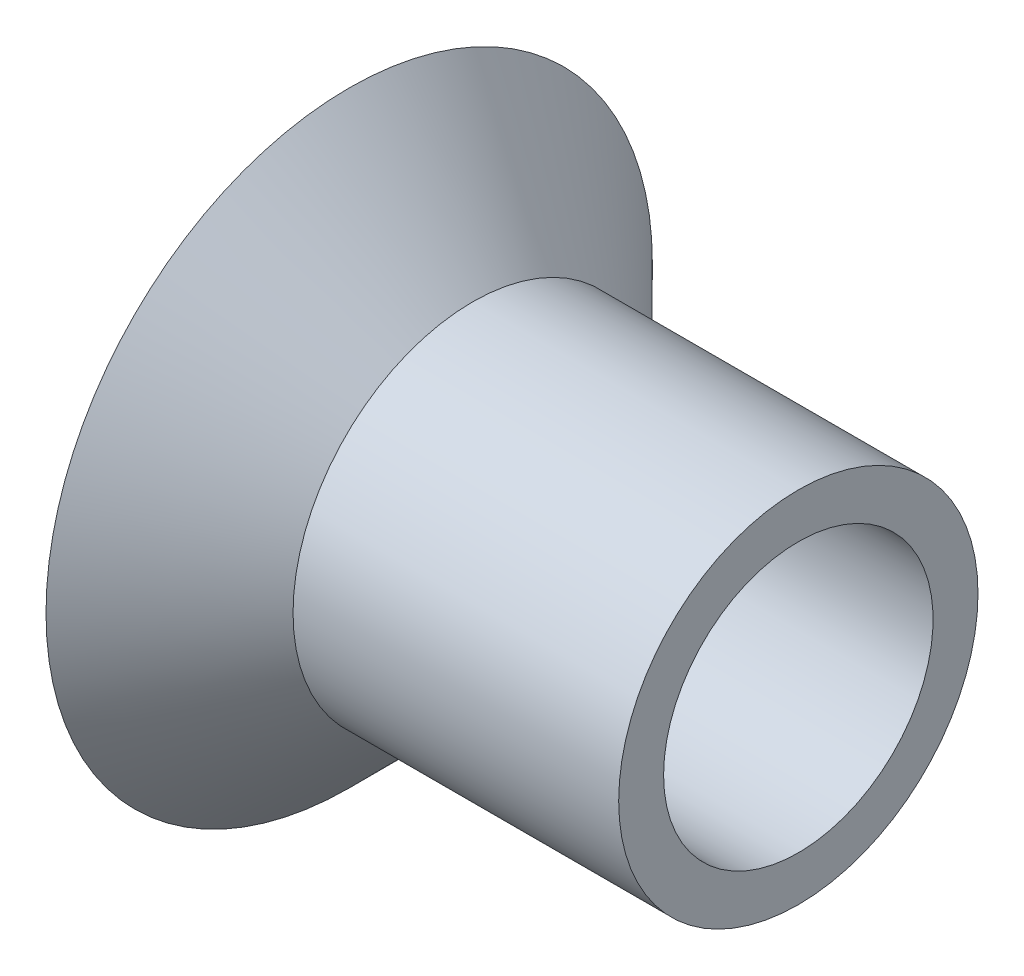
SolidWorks part; units mm, degrees
ref_plane "Front Plane" through (0, 0, 0) normal (0, 0, 1) x (1, 0, 0)
ref_plane "Top Plane" through (0, 0, 0) normal (0, 1, 0) x (1, 0, 0)
ref_plane "Right Plane" through (0, 0, 0) normal (1, 0, 0) x (0, 0, -1)
sketch "Sketch1" plane through (0, 0, 0) normal (0, 0, 1) x (1, 0, 0)
  line L0 (-9.5796, 0) -> (8.3541, 0) construction
  line L1 (-5, -6.75) -> (5, -6.75) construction
  line L2 (-5, -6.75) -> (-5, 6.75) construction
  line L3 (-5, 6.75) -> (5, 6.75) construction
  line L4 (5, -6.75) -> (5, 6.75) construction
  line L5 (-5, -6.75) -> (5, 6.75) construction
  line L6 (-5, 6.75) -> (5, -6.75) construction
  line L7 (5, 0) -> (5, 4) construction
  line L8 (5, 4) -> (-2.25, 4)
  line L9 (-2.25, 4) -> (-5, 6.75)
  line L10 (5, 3) -> (-2.6642, 3)
  line L11 (-2.6642, 3) -> (-5, 5.3358)
  line L12 (-5, 6.75) -> (-5, 5.3358)
  line L13 (5, 4) -> (5, 3)
  line L14 (-2.6642, 3) -> (-5.7071, 6.0429) construction
  point P0 (0, 0)
  dimension "D1" = 10
  dimension "D2" = 13.5
  dimension "D3" = 4
  dimension "D4" = 45
  dimension "D5" = 1
revolve "Revolve1" add sketch "Sketch1" angle 360 about L0
